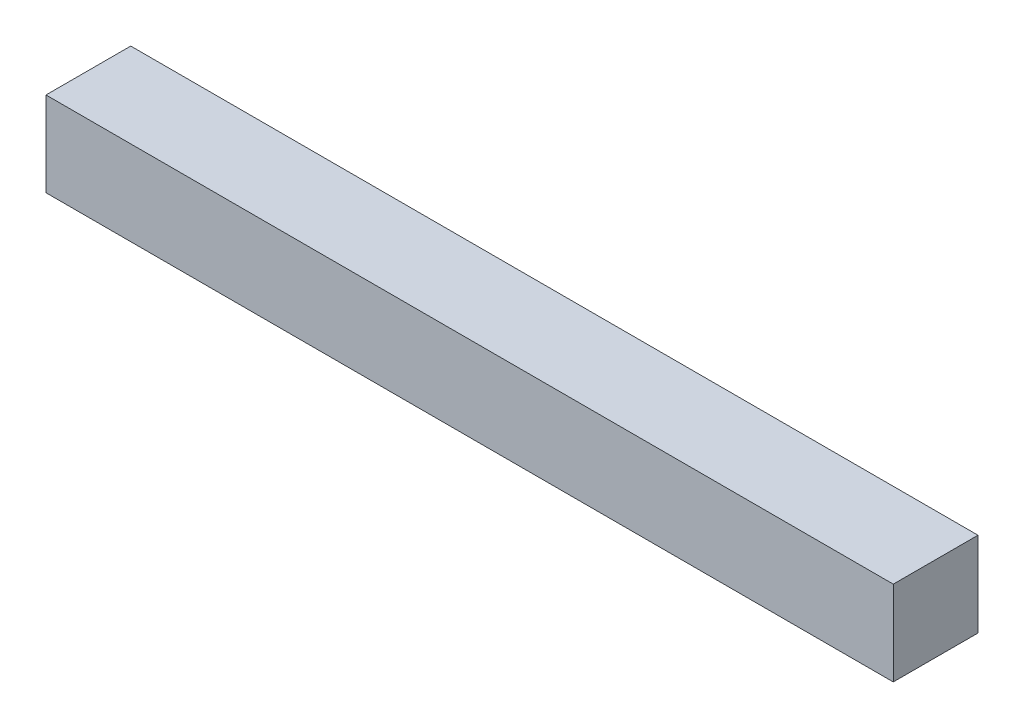
SolidWorks part; units mm, degrees
ref_plane "Plan de face" through (0, 0, 0) normal (0, 0, 1) x (1, 0, 0)
ref_plane "Plan de dessus" through (0, 0, 0) normal (0, 1, 0) x (1, 0, 0)
ref_plane "Plan de droite" through (0, 0, 0) normal (1, 0, 0) x (0, 0, -1)
sketch "Esquisse1" plane through (0, 0, 0) normal (0, 0, 1) x (1, 0, 0)
  line L1 (-68.6267, 15.3516) -> (231.3733, 15.3516)
  line L2 (-68.6267, 15.3516) -> (-68.6267, -14.6484)
  line L3 (-68.6267, -14.6484) -> (231.3733, -14.6484)
  line L4 (231.3733, 15.3516) -> (231.3733, -14.6484)
  dimension "D1" = 30
  dimension "D2" = 300
extrude "Boss.-Extru.4" add sketch "Esquisse1" along normal blind 30
sketch "Esquisse3" plane through (0, 0, 0) normal (0, 0, 1) x (1, 0, 0)
  line L0 (-53.6267, 15.3516) -> (-53.6267, -14.6484) construction
  line L1 (231.3733, 15.3516) -> (-68.6267, 15.3516) construction
  line L2 (-68.6267, -14.6484) -> (231.3733, -14.6484) construction
  line L3 (-68.6267, 15.3516) -> (-68.6267, -14.6484) construction
  circle A0 centre (-53.6267, 0.3516) radius 6
  circle A1 centre (-23.6267, 0.3516) radius 6
  circle A2 centre (6.3733, 0.3516) radius 6
  circle A3 centre (36.3733, 0.3516) radius 6
  circle A4 centre (66.3733, 0.3516) radius 6
  circle A5 centre (96.3733, 0.3516) radius 6
  circle A6 centre (126.3733, 0.3516) radius 6
  circle A7 centre (156.3733, 0.3516) radius 6
  circle A8 centre (186.3733, 0.3516) radius 6
  circle A9 centre (216.3733, 0.3516) radius 6
  dimension "D2" = 12
  dimension "D1" = 15
  dimension "D3" = 10
extrude "Enlèv. mat.-Extru.1" cut sketch "Esquisse3" along normal blind 10
